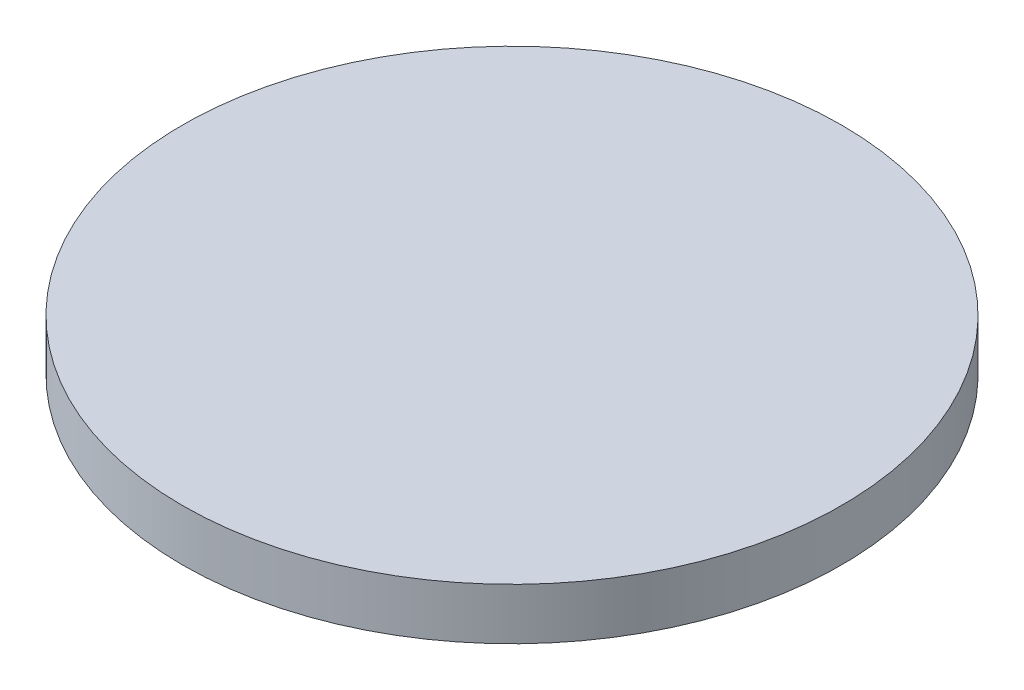
SolidWorks part; units mm, degrees
material "Thornel Mat VMA"
ref_plane "Front Plane" through (0, 0, 0) normal (0, 0, 1) x (1, 0, 0)
ref_plane "Top Plane" through (0, 0, 0) normal (0, 1, 0) x (1, 0, 0)
ref_plane "Right Plane" through (0, 0, 0) normal (1, 0, 0) x (0, 0, -1)
sketch "Sketch1" plane through (0, 0, 0) normal (0, 1, 0) x (1, 0, 0)
  circle A0 centre (0, 0) radius 20.32
  dimension "D1" = 40.64
extrude "Boss-Extrude1" add sketch "Sketch1" along normal blind 3.175
